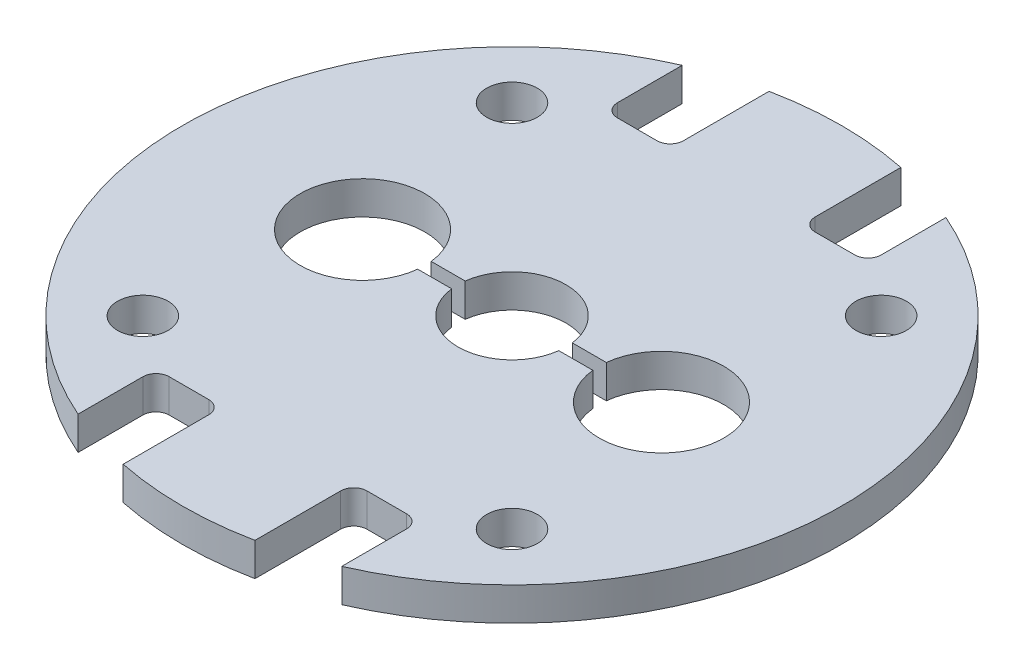
SolidWorks part; units mm, degrees
material "C110 COPPER"
ref_plane "Front Plane" through (0, 0, 0) normal (0, 0, 1) x (1, 0, 0)
ref_plane "Top Plane" through (0, 0, 0) normal (0, 1, 0) x (1, 0, 0)
ref_plane "Right Plane" through (0, 0, 0) normal (1, 0, 0) x (0, 0, -1)
sketch "Sketch1" plane through (0, 0, 0) normal (0, 1, 0) x (1, 0, 0)
  line L0 (-6.35, 14.5497) -> (-6.35, 11.43)
  line L1 (-5.715, 10.795) -> (-3.81, 10.795)
  line L2 (-3.175, 11.43) -> (-3.175, 15.5543)
  line L3 (0, 22.1967) -> (0, -24.306) construction
  line L4 (-23.8315, 0) -> (25.6492, 0) construction
  line L5 (3.175, 11.43) -> (3.175, 15.5543)
  line L6 (5.715, 10.795) -> (3.81, 10.795)
  line L7 (6.35, 14.5497) -> (6.35, 11.43)
  line L8 (6.35, -14.5497) -> (6.35, -11.43)
  line L9 (5.715, -10.795) -> (3.81, -10.795)
  line L10 (3.175, -11.43) -> (3.175, -15.5543)
  line L11 (-3.175, -11.43) -> (-3.175, -15.5543)
  line L12 (-5.715, -10.795) -> (-3.81, -10.795)
  line L13 (-6.35, -14.5497) -> (-6.35, -11.43)
  arc A0 (-6.35, 14.5497) -> (-6.35, -14.5497) centre (0, 0) ccw
  arc A1 (-3.81, 10.795) -> (-3.175, 11.43) centre (-3.81, 11.43) ccw
  arc A2 (-6.35, 11.43) -> (-5.715, 10.795) centre (-5.715, 11.43) ccw
  arc A3 (6.35, 11.43) -> (5.715, 10.795) centre (5.715, 11.43) cw
  arc A4 (3.81, 10.795) -> (3.175, 11.43) centre (3.81, 11.43) cw
  arc A5 (3.81, -10.795) -> (3.175, -11.43) centre (3.81, -11.43) ccw
  arc A6 (6.35, -11.43) -> (5.715, -10.795) centre (5.715, -11.43) ccw
  arc A7 (-6.35, -11.43) -> (-5.715, -10.795) centre (-5.715, -11.43) cw
  arc A8 (-3.81, -10.795) -> (-3.175, -11.43) centre (-3.81, -11.43) cw
  arc A9 (3.175, 15.5543) -> (-3.175, 15.5543) centre (0, 0) ccw
  arc A10 (6.35, -14.5497) -> (6.35, 14.5497) centre (0, 0) ccw
  arc A11 (-3.175, -15.5543) -> (3.175, -15.5543) centre (0, 0) ccw
  dimension "D1" = 31.75
  dimension "D5" = 0.635
  dimension "D2" = 3.175
  dimension "D3" = 6.35
  dimension "D4" = 10.795
extrude "Boss-Extrude1" add sketch "Sketch1" along normal mid plane 1.6
sketch "Sketch2" plane through (0, 0.8, 0) normal (0, 1, 0) x (1, 0, 0)
  line L0 (-19.5403, 0) -> (21.377, 0) construction
  line L1 (-4.2177, 0.325) -> (-2.5796, 0.325)
  line L2 (-4.2177, -0.325) -> (-2.5796, -0.325)
  line L3 (2.5796, 0.325) -> (4.2177, 0.325)
  line L4 (2.5796, -0.325) -> (4.2177, -0.325)
  arc A0 (-4.2177, 0.325) -> (-4.2177, -0.325) centre (-7.2, 0) ccw
  arc A1 (-2.5796, -0.325) -> (2.5796, -0.325) centre (0, 0) ccw
  arc A2 (4.2177, -0.325) -> (4.2177, 0.325) centre (7.2, 0) ccw
  arc A3 (2.5796, 0.325) -> (-2.5796, 0.325) centre (0, 0) ccw
  dimension "D1" = 5.2
  dimension "D2" = 6
  dimension "D3" = 7.2
  dimension "D4" = 7.2
  dimension "D5" = 0.65
extrude "Cut-Extrude1" cut sketch "Sketch2" against normal through all
hole_wizard "#2 Clearance Hole1" positions "Sketch4" profile "Sketch5" hole size "#2" standard "ANSI Inch" end condition up to next
sketch "Sketch4" plane through (0, 0.8, 0) normal (0, 1, 0) x (1, 0, 0)
  line L1 (-8.89, 8.89) -> (8.89, 8.89)
  line L2 (-8.89, 8.89) -> (-8.89, -8.89)
  line L3 (-8.89, -8.89) -> (8.89, -8.89)
  line L4 (8.89, 8.89) -> (8.89, -8.89)
  line L5 (-8.89, 8.89) -> (8.89, -8.89) construction
  line L6 (-8.89, -8.89) -> (8.89, 8.89) construction
  point P0 (-8.89, 8.89)
  point P2 (8.89, 8.89)
  point P4 (-8.89, -8.89)
  point P6 (8.89, -8.89)
  point P58 (0, 0)
  dimension "D1" = 17.78
  dimension "D2" = 17.78
sketch "Sketch5" plane through (-8.89, 0.8, -8.89) normal (1, 0, 0) x (0, 0, 1)
  line L0 (0, 0) -> (0, 1.6)
  line L1 (0, 1.6) -> (1.2192, 1.6)
  line L2 (1.2192, 1.6) -> (1.2192, 0)
  line L5 (1.2192, 0) -> (0, 0)
  line L11 (0, -6.35) -> (0, 107.95) construction
  dimension "Thru Hole Dia." = 2.4384
  dimension "Thru Hole Depth" = 1.6
